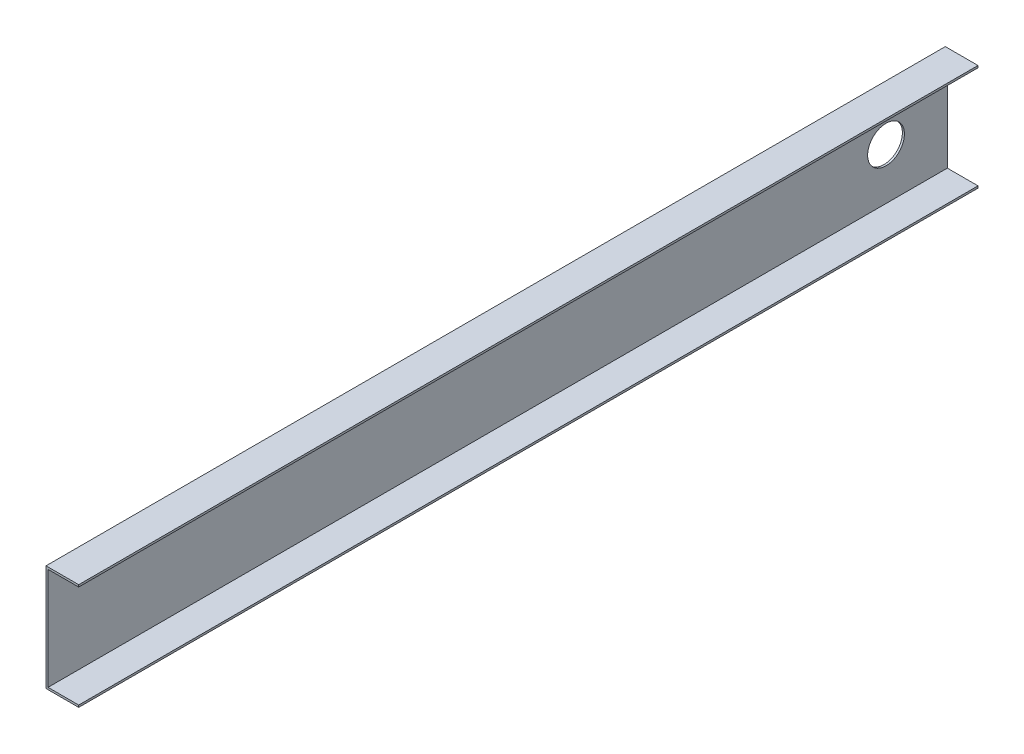
SolidWorks part; units mm, degrees
material "1.4000 (X6Cr13)"
ref_plane "Plano frontal" through (0, 0, 0) normal (0, 0, 1) x (1, 0, 0)
ref_plane "Plano superior" through (0, 0, 0) normal (0, 1, 0) x (1, 0, 0)
ref_plane "Plano direito" through (0, 0, 0) normal (1, 0, 0) x (0, 0, -1)
sketch "Esboço1" plane through (0, 0, 0) normal (0, 0, 1) x (1, 0, 0)
  line L0 (8, 13) -> (0, 13)
  line L1 (0, 13) -> (0, -13)
  line L2 (0, -13) -> (8, -13)
  line L3 (8, 12.5) -> (0.5, 12.5)
  line L4 (0.5, 12.5) -> (0.5, -12.5)
  line L5 (0.5, -12.5) -> (8, -12.5)
  line L6 (8, 13) -> (8, 12.5)
  line L7 (8, -13) -> (8, -12.5)
  point P6 (0, 0)
  dimension "D1" = 26
  dimension "D2" = 8
  dimension "D3" = 0.5
extrude "Ressalto-extrusão1" add sketch "Esboço1" along normal blind 220
sketch "Esboço2" plane through (0, 0, 0) normal (-1, 0, 0) x (0, 0, 1)
  circle A0 centre (15, 0) radius 4.5
  dimension "D1" = 15
  dimension "D2" = 9
extrude "Corte-extrusão1" cut sketch "Esboço2" against normal blind 10
